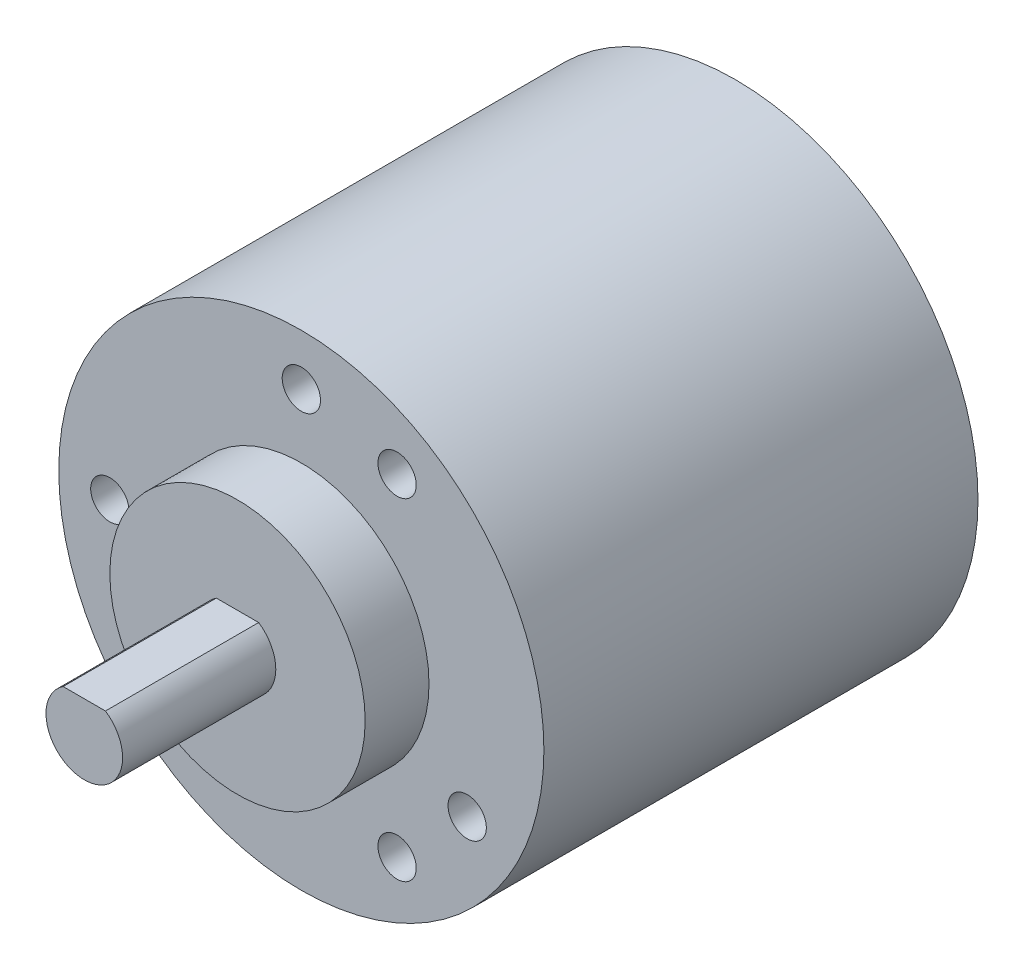
SolidWorks part; units mm, degrees
ref_plane "Front Plane" through (0, 0, 0) normal (0, 0, 1) x (1, 0, 0)
ref_plane "Top Plane" through (0, 0, 0) normal (0, 1, 0) x (1, 0, 0)
ref_plane "Right Plane" through (0, 0, 0) normal (1, 0, 0) x (0, 0, -1)
sketch "Sketch1" plane through (0, 0, 0) normal (0, 0, 1) x (1, 0, 0)
  circle A0 centre (0, 0) radius 19
  dimension "D1" = 38
extrude "Boss-Extrude1" add sketch "Sketch1" along normal blind 34
sketch "Sketch2" plane through (0, 0, 34) normal (0, 0, 1) x (1, 0, 0)
  line L0 (0, 15) -> (0, 0) construction
  line L1 (0, 0) -> (7.5, 12.9904) construction
  circle A0 centre (0, 0) radius 10
  circle A1 centre (0, 0) radius 15 construction
  circle A2 centre (0, 15) radius 1.5
  circle A3 centre (7.5, 12.9904) radius 1.5
  circle A4 centre (7.5, -12.9904) radius 1.5
  circle A5 centre (12.9904, -7.5) radius 1.5
  circle A6 centre (-15, 0) radius 1.5
  circle A7 centre (-12.9904, -7.5) radius 1.5
  point P18 (0, 0)
  dimension "D1" = 20
  dimension "D2" = 30
  dimension "D3" = 3
  dimension "D4" = 30
  dimension "D5" = 3
extrude "Cut-Extrude1" cut sketch "Sketch2" against normal blind 6 contours A7 | A6 | A2 | A3 | A5 | A4
sketch "Sketch3" plane through (0, 0, 34) normal (0, 0, 1) x (1, 0, 0)
  circle A0 centre (0, 0) radius 10
  dimension "D1" = 20
extrude "Boss-Extrude2" add sketch "Sketch3" along normal blind 5
sketch "Sketch4" plane through (0, 0, 39) normal (0, 0, 1) x (1, 0, 0)
  line L0 (1.6583, 2.5) -> (-1.6583, 2.5)
  circle A0 centre (0, 0) radius 3
  dimension "D1" = 6
  dimension "D2" = 2.5
extrude "Boss-Extrude3" add sketch "Sketch4" along normal blind 12 contours L0 A0
